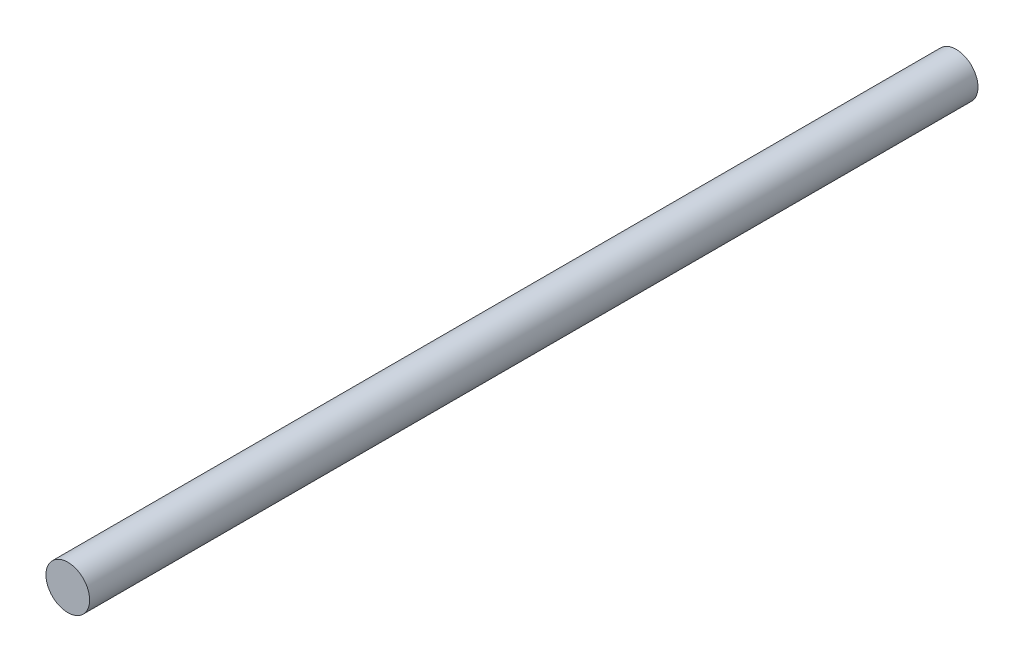
SolidWorks part; units mm, degrees
material "AISI 304"
ref_plane "前视基准面" through (0, 0, 0) normal (0, 0, 1) x (1, 0, 0)
ref_plane "上视基准面" through (0, 0, 0) normal (0, 1, 0) x (1, 0, 0)
ref_plane "右视基准面" through (0, 0, 0) normal (1, 0, 0) x (0, 0, -1)
sketch "Sketch1" plane through (0, 0, 0) normal (0, 0, 1) x (1, 0, 0)
  circle A0 centre (0, 0) radius 3
  dimension "D1" = 6
extrude "Boss-Extrude1" add sketch "Sketch1" along normal blind 122
